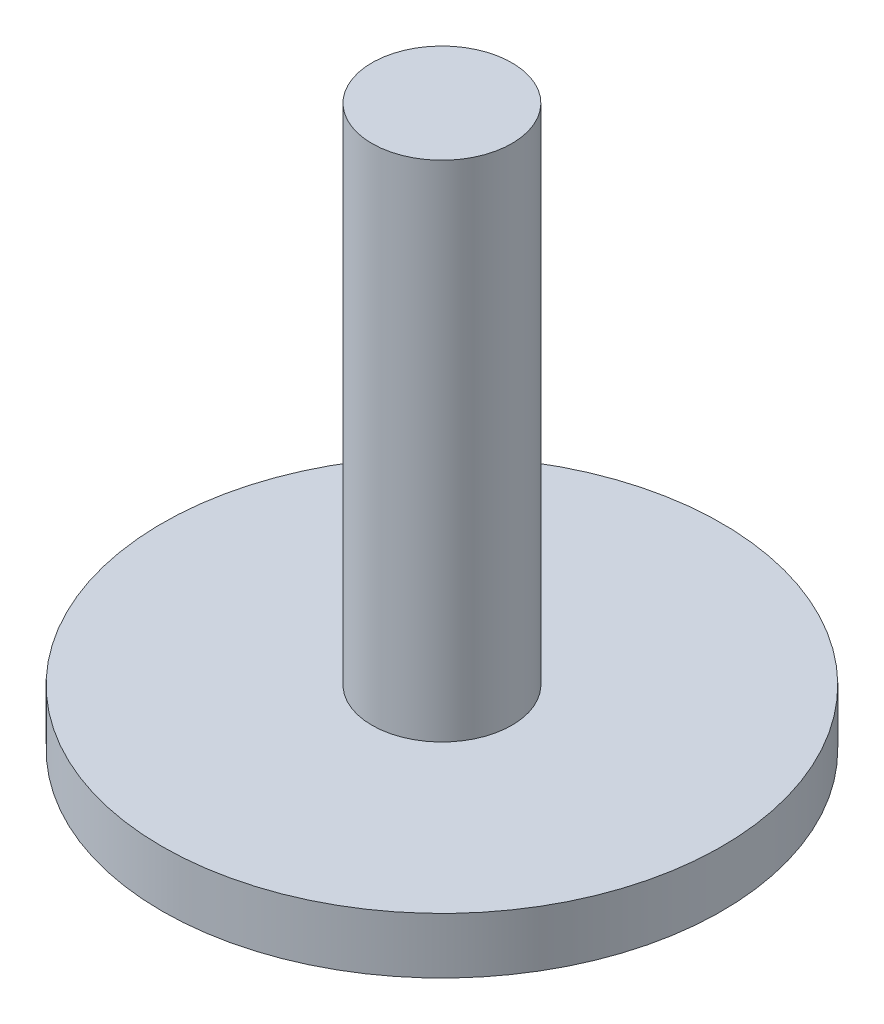
SolidWorks part; units mm, degrees
ref_plane "Front Plane" through (0, 0, 0) normal (0, 0, 1) x (1, 0, 0)
ref_plane "Top Plane" through (0, 0, 0) normal (0, 1, 0) x (1, 0, 0)
ref_plane "Right Plane" through (0, 0, 0) normal (1, 0, 0) x (0, 0, -1)
sketch "Center Shaft" plane through (0, 0, 0) normal (0, 1, 0) x (1, 0, 0)
  circle A0 centre (0, 0) radius 0.635
sketch "Top Landing" plane through (0, 0, 0) normal (0, 1, 0) x (1, 0, 0)
  circle A0 centre (0, 0) radius 2.54
extrude "Center Shaft extr" add sketch "Center Shaft" along normal blind 5.08
extrude "Top landing extr" add sketch "Top Landing" along normal blind 0.508
sketch "Alignment lines" plane through (0, 0, 0) normal (0, -1, 0) x (-1, 0, 0)
  line L0 (0, -0.635) -> (0, -2.54)
  line L1 (-0.635, 0) -> (-2.54, 0)
  line L2 (0, 0.635) -> (0, 2.54)
  line L3 (0.635, 0) -> (2.54, 0)
  line L4 (0, 0) -> (-1.7961, -1.7961)
  line L5 (0, 0) -> (1.7961, -1.7961)
  line L6 (0, 0) -> (-1.7961, 1.7961)
  line L7 (0, 0) -> (1.7961, 1.7961)
  line L8 (0, 0) -> (-0.972, -2.3467)
  line L9 (0, 0) -> (0.972, 2.3467)
  line L10 (0, 0) -> (-2.3467, 0.972)
  line L11 (0, 0) -> (2.3467, -0.972)
  line L12 (0, 0) -> (0.972, -2.3467)
  line L13 (0.972, -2.3467) -> (-0.972, 2.3467)
  line L14 (0, 0) -> (2.3467, 0.972)
  line L15 (2.3467, 0.972) -> (-2.3467, -0.972)
  circle A0 centre (0, 0) radius 0.635 construction
  circle A1 centre (0, 0) radius 2.54 construction
sketch "Sketch12" plane through (0, 0, 0) normal (0, -1, 0) x (-1, 0, 0)
  line L0 (0, 0) -> (-0.972, -2.3467) construction
  line L1 (0, 0) -> (-0.3596, -0.8683) construction
  circle A0 centre (-0.3596, -0.8683) radius 0.1524
  circle A1 centre (-0.8683, -0.3596) radius 0.1524
  circle A2 centre (-0.8683, 0.3596) radius 0.1524
  circle A3 centre (-0.3596, 0.8683) radius 0.1524
  circle A4 centre (0.3596, 0.8683) radius 0.1524
  circle A5 centre (0.8683, 0.3596) radius 0.1524
  circle A6 centre (0.8683, -0.3596) radius 0.1524
  circle A7 centre (0.3596, -0.8683) radius 0.1524
  dimension "D1" = 0.9398
  dimension "D3" = 0.9398
  dimension "D2" = 8
sketch "Sketch13" plane through (0, 0, 0) normal (0, -1, 0) x (-1, 0, 0)
  line L0 (0, 0) -> (-1.7961, -1.7961) construction
  line L1 (0, 0) -> (-0.9946, -0.9946) construction
  circle A0 centre (-0.9946, -0.9946) radius 0.1524
  circle A1 centre (-1.3587, -0.3641) radius 0.1524
  circle A2 centre (-1.3587, 0.3641) radius 0.1524
  circle A3 centre (-0.9946, 0.9946) radius 0.1524
  circle A4 centre (-0.3641, 1.3587) radius 0.1524
  circle A5 centre (0.3641, 1.3587) radius 0.1524
  circle A6 centre (0.9946, 0.9946) radius 0.1524
  circle A7 centre (1.3587, 0.3641) radius 0.1524
  circle A8 centre (1.3587, -0.3641) radius 0.1524
  circle A9 centre (0.9946, -0.9946) radius 0.1524
  circle A10 centre (0.3641, -1.3587) radius 0.1524
  circle A11 centre (-0.3641, -1.3587) radius 0.1524
  dimension "D1" = 0.635
  dimension "D2" = 12
  dimension "D3" = 1.4066
sketch "Sketch14" plane through (0, 0, 0) normal (0, -1, 0) x (-1, 0, 0)
  line L0 (0, 0) -> (-0.972, -2.3467) construction
  line L1 (0, 0) -> (-0.6939, -1.6753) construction
  circle A0 centre (-0.6939, -1.6753) radius 0.1524
  circle A1 centre (-1.2822, -1.2822) radius 0.1524
  circle A2 centre (-1.6753, -0.6939) radius 0.1524
  circle A3 centre (-1.8133, 0) radius 0.1524
  circle A4 centre (-1.6753, 0.6939) radius 0.1524
  circle A5 centre (-1.2822, 1.2822) radius 0.1524
  circle A6 centre (-0.6939, 1.6753) radius 0.1524
  circle A7 centre (0, 1.8133) radius 0.1524
  circle A8 centre (0.6939, 1.6753) radius 0.1524
  circle A9 centre (1.2822, 1.2822) radius 0.1524
  circle A10 centre (1.6753, 0.6939) radius 0.1524
  circle A11 centre (1.8133, 0) radius 0.1524
  circle A12 centre (1.6753, -0.6939) radius 0.1524
  circle A13 centre (1.2822, -1.2822) radius 0.1524
  circle A14 centre (0.6939, -1.6753) radius 0.1524
  circle A15 centre (0, -1.8133) radius 0.1524
  dimension "D1" = 0.4572
  dimension "D3" = 1.8133
  dimension "D2" = 16
